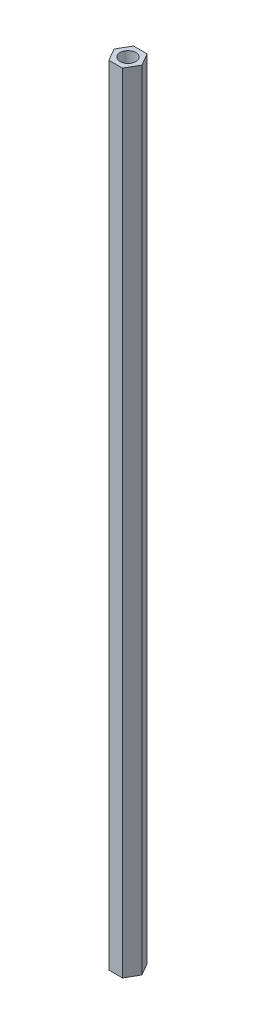
SolidWorks part; units mm, degrees
ref_plane "前视基准面" through (0, 0, 0) normal (0, 0, 1) x (1, 0, 0)
ref_plane "上视基准面" through (0, 0, 0) normal (0, 1, 0) x (1, 0, 0)
ref_plane "右视基准面" through (0, 0, 0) normal (1, 0, 0) x (0, 0, -1)
sketch "草图1" plane through (0, 0, 0) normal (0, 1, 0) x (1, 0, 0)
  line L0 (-12.6472, 0) -> (11.4268, 0) construction
  line L1 (0, 12.1757) -> (0, -13.2296) construction
  line L2 (1.2932, 2.35) -> (-1.2932, 2.35)
  line L7 (1.2932, -2.35) -> (-1.2932, -2.35)
  line L8 (1.2932, 2.35) -> (2.65, 0)
  line L9 (-1.2932, 2.35) -> (-2.65, 0)
  line L10 (1.2932, -2.35) -> (2.65, 0)
  line L11 (-1.2932, -2.35) -> (-2.65, 0)
  circle A0 centre (0, 0) radius 1.5
  point P12 (0, 2.35)
  dimension "D1" = 3
  dimension "D2" = 5.3
  dimension "D3" = 4.7
  dimension "D4" = 120
extrude "凸台-拉伸1" add sketch "草图1" along normal blind 150
